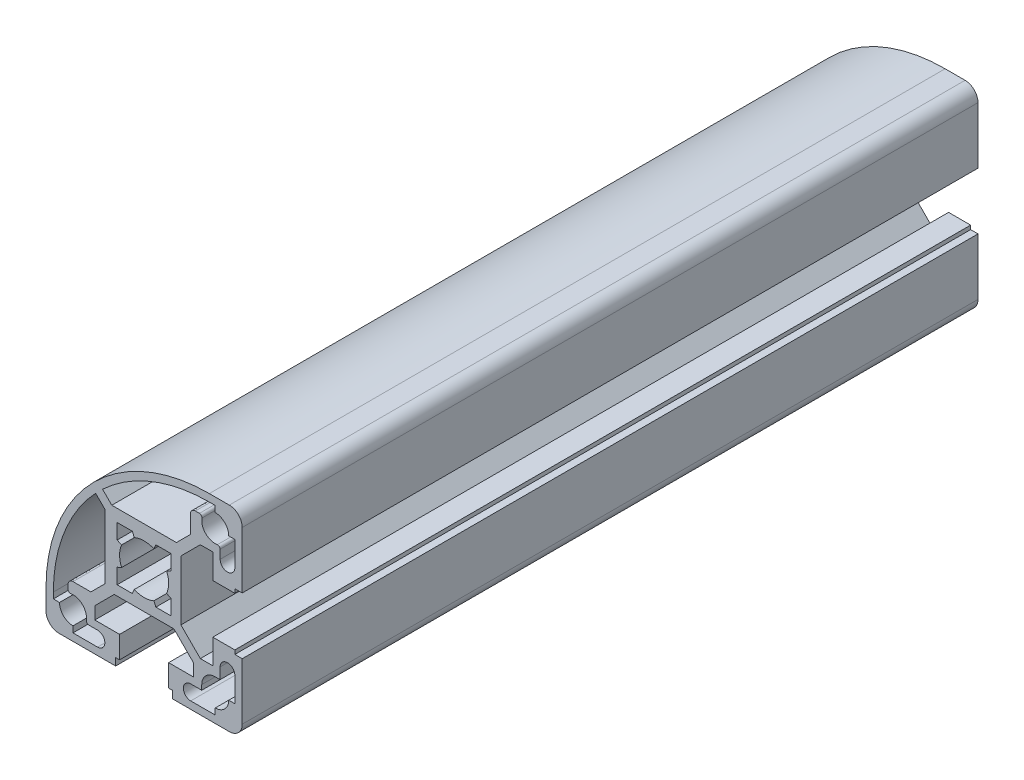
SolidWorks part; units mm, degrees
ref_plane "Front Plane" through (0, 0, 0) normal (0, 0, 1) x (1, 0, 0)
ref_plane "Top Plane" through (0, 0, 0) normal (0, 1, 0) x (1, 0, 0)
ref_plane "Right Plane" through (0, 0, 0) normal (1, 0, 0) x (0, 0, -1)
sketch "Sketch2" plane through (0, 0, 0) normal (0, 0, 1) x (1, 0, 0)
  line L0 (-24.0529, 24.0529) -> (24.0529, -24.0529) construction
  line L1 (0, 12.4053) -> (0, -11.4642) construction
  line L2 (21.3076, -13.3) -> (-24.0529, -13.3) construction
  line L3 (18.5, -5.8) -> (18.5, -5)
  line L4 (2.3979, 5.5) -> (1.9983, 4.5833)
  line L5 (9.4383, 10.8525) -> (6.5858, 8)
  line L6 (-6.5858, 8) -> (6.5858, 8)
  line L7 (-8.4678, 9.882) -> (-6.5858, 8)
  line L8 (-5.5, 5.5) -> (-2.3979, 5.5)
  line L9 (5.5, 5.5) -> (2.3979, 5.5)
  line L10 (5.5, 5.5) -> (5.5, 2.3979)
  line L11 (5.5, -5.5) -> (5.5, -2.3979)
  line L12 (-2.3979, 5.5) -> (-1.9983, 4.5833)
  line L13 (11.75, -15.5) -> (11.75, -14.5)
  line L14 (5.5, -2.3979) -> (4.5833, -1.9983)
  line L15 (5.5, 2.3979) -> (4.5833, 1.9983)
  line L16 (17.3692, 20) -> (13.3, 20)
  line L17 (14.5, 18.5006) -> (14.5, 17.25)
  line L18 (14.5, -18.5) -> (14.5, -17.25)
  line L19 (14.5, -18.5) -> (9.5, -18.5)
  line L20 (9.5, -15.5) -> (11.75, -15.5)
  line L21 (10.05, -14) -> (5, -14)
  line L22 (5, -14) -> (5, -18.5)
  line L23 (5.8, -18.5) -> (5.8, -20)
  line L24 (5.8, -20) -> (17.3692, -20)
  line L25 (18.5, 14.5) -> (17.25, 14.5)
  line L26 (18.5, 14.5) -> (18.5, 9.5)
  line L27 (15.5, 11.2887) -> (15.5, 9.5)
  line L28 (10.4383, 15.5) -> (11.2887, 15.5)
  line L29 (9.4383, 14.5) -> (9.4383, 10.8525)
  line L30 (14.5, 18.5006) -> (13.2839, 18.5)
  line L31 (11.4642, -10.05) -> (14, -10.05)
  line L32 (7.5, -6.0858) -> (11.4642, -10.05)
  line L33 (7.5, 6.0858) -> (7.5, -6.0858)
  line L34 (11.4642, 10.05) -> (7.5, 6.0858)
  line L35 (14, 10.05) -> (11.4642, 10.05)
  line L36 (14, 10.05) -> (14, 5)
  line L37 (18.5, 5) -> (14, 5)
  line L38 (18.5, 5.8) -> (18.5, 5)
  line L39 (20, 5.8) -> (18.5, 5.8)
  line L40 (20, 17.3692) -> (20, 5.8)
  line L41 (20, -5.8) -> (20, -17.3692)
  line L42 (-17.3692, -20) -> (-5.8, -20)
  line L43 (-5.8, -20) -> (-5.8, -18.5)
  line L44 (-5.8, -18.5) -> (-5, -18.5)
  line L45 (-5, -18.5) -> (-5, -14)
  line L46 (-10.05, -14) -> (-5, -14)
  line L47 (-10.05, -14) -> (-10.05, -11.4642)
  line L48 (-10.05, -11.4642) -> (-6.0858, -7.5)
  line L49 (-6.0858, -7.5) -> (6.0858, -7.5)
  line L50 (6.0858, -7.5) -> (10.05, -11.4642)
  line L51 (10.05, -11.4642) -> (10.05, -14)
  line L52 (18.5, -5.8) -> (20, -5.8)
  line L53 (14, -5) -> (18.5, -5)
  line L54 (14, -10.05) -> (14, -5)
  line L55 (15.5, -9.5) -> (15.5, -11.75)
  line L56 (18.5, -14.5) -> (18.5, -9.5)
  line L57 (18.5, -14.5) -> (17.25, -14.5)
  line L58 (15.5, -11.75) -> (14.5, -11.75)
  line L59 (13.3, -21.6848) -> (13.3, -2.8592) construction
  line L66 (-18.5006, -14.5) -> (-18.5, -13.2839)
  line L67 (-14.5, -9.4383) -> (-10.8525, -9.4383)
  line L68 (-15.5, -10.4383) -> (-15.5, -11.2887)
  line L69 (-11.2887, -15.5) -> (-9.5, -15.5)
  line L70 (-14.5, -18.5) -> (-9.5, -18.5)
  line L71 (-14.5, -18.5) -> (-14.5, -17.25)
  line L72 (-18.5006, -14.5) -> (-17.25, -14.5)
  line L73 (-20, -17.3692) -> (-20, -13.3)
  line L103 (-2.3979, -5.5) -> (-1.9983, -4.5833)
  line L104 (2.3979, -5.5) -> (1.9983, -4.5833)
  line L106 (-5.5, 2.3979) -> (-4.5833, 1.9983)
  line L112 (5.5, -5.5) -> (2.3979, -5.5)
  line L113 (-5.5, -5.5) -> (-2.3979, -5.5)
  line L114 (-5.5, -5.5) -> (-5.5, -2.3979)
  line L116 (-5.5, 5.5) -> (-5.5, 2.3979)
  line L119 (-9.882, 8.4678) -> (-8, 6.5858)
  line L120 (-8, 6.5858) -> (-8, -6.5858)
  line L121 (-10.8525, -9.4383) -> (-8, -6.5858)
  line L148 (-5.5, -2.3979) -> (-4.5833, -1.9983)
  line L150 (5.8, -18.5) -> (5, -18.5)
  line L151 (-20.6945, 0) -> (24.9984, 0) construction
  arc A0 (-1.9983, 4.5833) -> (1.9983, 4.5833) centre (0, 0) cw
  arc A1 (4.5833, 1.9983) -> (4.5833, -1.9983) centre (0, 0) cw
  arc A2 (17.3692, 20) -> (20, 17.3692) centre (17.3692, 17.3692) cw
  arc A3 (14.5, 17.25) -> (17.25, 14.5) centre (14.5, 14.5) cw
  arc A4 (18.5, 9.5) -> (15.5, 9.5) centre (17, 9.5) cw
  arc A5 (14.5, -11.75) -> (11.75, -14.5) centre (14.5, -14.5) ccw
  arc A6 (14.9231, 11.7827) -> (15.5, 11.2887) centre (15, 11.2887) cw
  arc A7 (14.5, -17.25) -> (17.25, -14.5) centre (14.5, -14.5) ccw
  arc A8 (9.5, -15.5) -> (9.5, -18.5) centre (9.5, -17) ccw
  arc A9 (17.3692, -20) -> (20, -17.3692) centre (17.3692, -17.3692) ccw
  arc A10 (14.9231, 11.7827) -> (11.7827, 14.9231) centre (14.5, 14.5) cw
  arc A11 (11.2887, 15.5) -> (11.7827, 14.9231) centre (11.2887, 15) cw
  arc A12 (9.4383, 14.5) -> (10.4383, 15.5) centre (10.4383, 14.5) cw
  arc A13 (-8.4678, 9.882) -> (13.2839, 18.5) centre (13.3, -13.3) cw
  arc A14 (15.5, -9.5) -> (18.5, -9.5) centre (17, -9.5) cw
  arc A19 (-9.882, 8.4678) -> (-18.5, -13.2839) centre (13.3, -13.3) ccw
  arc A20 (-14.5, -9.4383) -> (-15.5, -10.4383) centre (-14.5, -10.4383) ccw
  arc A21 (-15.5, -11.2887) -> (-14.9231, -11.7827) centre (-15, -11.2887) ccw
  arc A22 (-11.7827, -14.9231) -> (-14.9231, -11.7827) centre (-14.5, -14.5) ccw
  arc A23 (-11.7827, -14.9231) -> (-11.2887, -15.5) centre (-11.2887, -15) ccw
  arc A24 (-9.5, -18.5) -> (-9.5, -15.5) centre (-9.5, -17) ccw
  arc A25 (-17.25, -14.5) -> (-14.5, -17.25) centre (-14.5, -14.5) ccw
  arc A26 (13.3, 20) -> (-20, -13.3) centre (13.3, -13.3) ccw
  arc A27 (-20, -17.3692) -> (-17.3692, -20) centre (-17.3692, -17.3692) ccw
  arc A34 (-1.9983, -4.5833) -> (1.9983, -4.5833) centre (0, 0) ccw
  arc A36 (-4.5833, 1.9983) -> (-4.5833, -1.9983) centre (0, 0) ccw
  dimension "D3" = 33.3
  dimension "D4" = 10
  dimension "D1" = 6.7
  dimension "D2" = 40
  dimension "D5" = 40
  dimension "D6" = 6.7
extrude "Extrude1" add sketch "Sketch2" against normal blind 150
